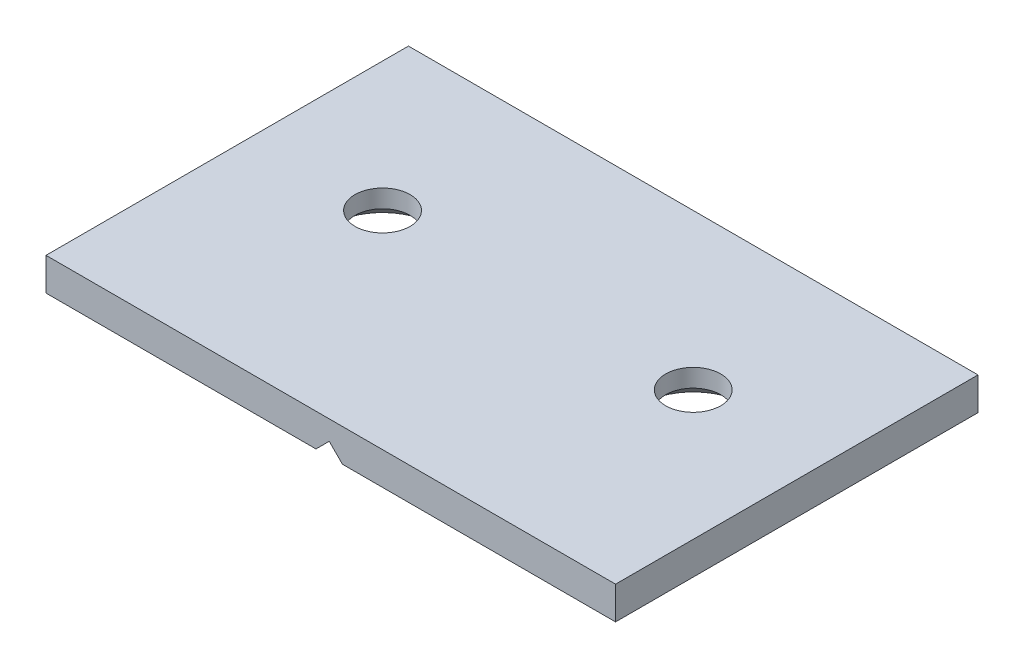
SolidWorks part; units mm, degrees
ref_plane "Front Plane" through (0, 0, 0) normal (0, 0, 1) x (1, 0, 0)
ref_plane "Top Plane" through (0, 0, 0) normal (0, 1, 0) x (1, 0, 0)
ref_plane "Right Plane" through (0, 0, 0) normal (1, 0, 0) x (0, 0, -1)
sketch "Sketch2" plane through (0, 0, 0) normal (0, 1, 0) x (1, 0, 0)
  line L1 (-33.844, 21.3431) -> (36.006, 21.3431)
  line L2 (-33.844, 21.3431) -> (-33.844, -23.1069)
  line L3 (-33.844, -23.1069) -> (36.006, -23.1069)
  line L4 (36.006, 21.3431) -> (36.006, -23.1069)
  dimension "D1" = 69.85
  dimension "D2" = 44.45
extrude "Boss-Extrude1" add sketch "Sketch2" along normal blind 4.7752
sketch "Sketch3" plane through (0, 0, -21.3431) normal (0, 0, -1) x (-1, 0, 0)
  line L0 (-0.8887, 2.3876) -> (-3.4638, -0.1875)
  line L2 (-36.006, 4.7752) -> (33.844, 4.7752) construction
  line L3 (-0.8887, 2.3876) -> (1.6864, -0.1875)
  line L4 (-3.4638, -0.1875) -> (1.6864, -0.1875)
  dimension "D2" = 90
extrude "Cut-Extrude1" cut sketch "Sketch3" against normal through all both and the other way through all
chamfer "Chamfer1" distance 0.762 angle 45 6 edges at (-17.6715, 0, -21.3431) (-33.844, 0, 0.8819) (-17.6715, 0, 23.1069) (19.6411, 0, 23.1069) (36.006, 0, 0.8819) (19.6411, 0, -21.3431)
sketch "Sketch6" plane through (0, 0, 0) normal (0, -1, 0) x (-1, 0, 0)
  line L0 (-36.006, -23.1069) -> (-36.006, 21.3431) construction
  line L1 (33.844, 21.3431) -> (33.844, -23.1069) construction
  line L2 (0.7369, 21.3431) -> (33.844, 21.3431) construction
  line L3 (-36.006, 21.3431) -> (-2.5143, 21.3431) construction
  point P0 (-20.131, 2.2931)
  point P2 (17.969, 2.2931)
  dimension "D1" = 15.875
  dimension "D2" = 15.875
  dimension "D3" = 19.05
  dimension "D4" = 19.05
hole_wizard "CSK for 1/4 Flat Head Machine Screw (100)1" positions "Sketch6" profile "Sketch5" countersink size "1/4" standard "ANSI Inch"
sketch "Sketch5" plane through (20.131, 0, -2.2931) normal (1, 0, 0) x (0, 0, -1)
  line L0 (0, 0) -> (0, 6.8558)
  line L1 (0, 6.8558) -> (3.3782, 4.826)
  line L2 (3.3782, 4.826) -> (3.3782, 2.5682)
  line L3 (3.3782, 2.5682) -> (6.4389, 0)
  line L5 (6.4389, 0) -> (0, 0)
  line L6 (-3.3782, 2.5682) -> (-6.4389, 0) construction
  line L10 (0, 6.8558) -> (-3.3782, 4.826) construction
  line L11 (0, -6.35) -> (0, 107.95) construction
  dimension "Hole Dia." = 6.7564
  dimension "Hole Depth" = 4.826
  dimension "Near C'Sink Dia." = 12.8778
  dimension "Near C'Sink Angle" = 100
  dimension "Drill Angle" = 118
